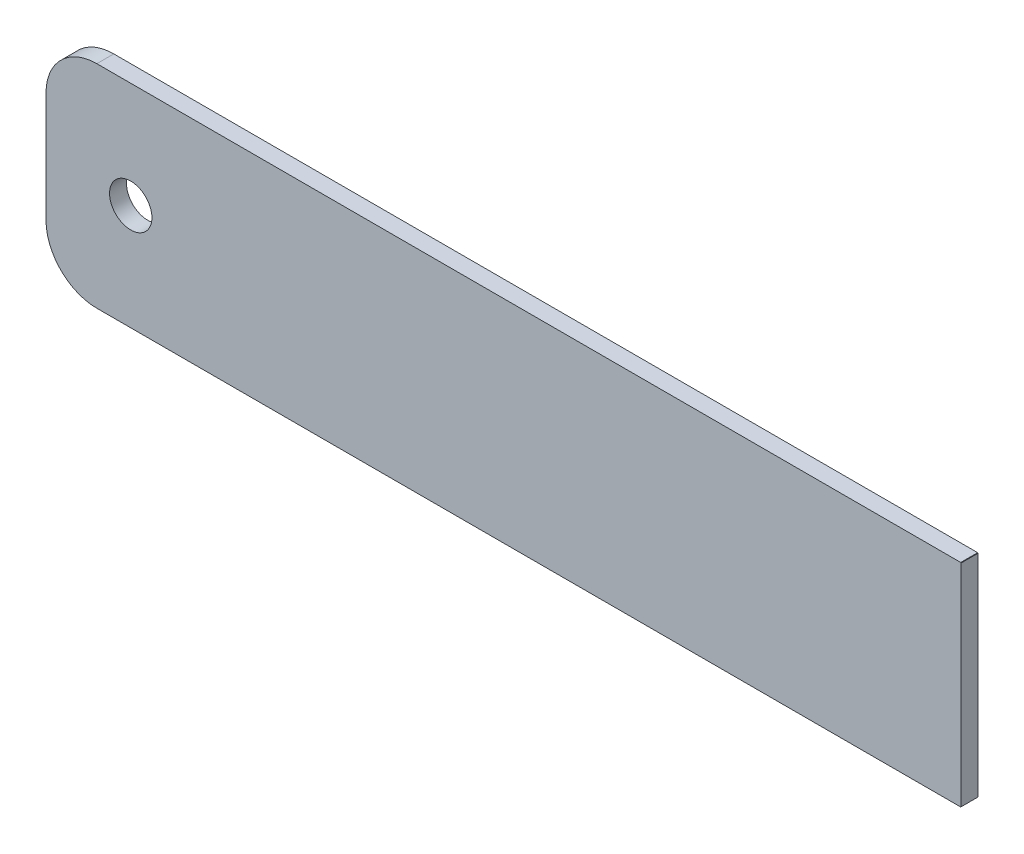
SolidWorks part; units mm, degrees
material "302 SSTL"
ref_plane "Front" through (0, 0, 0) normal (0, 0, 1) x (1, 0, 0)
ref_plane "Top" through (0, 0, 0) normal (0, 1, 0) x (1, 0, 0)
ref_plane "Right" through (0, 0, 0) normal (1, 0, 0) x (0, 0, -1)
sketch "Sketch1" plane through (0, 0, 0) normal (0, 0, 1) x (1, 0, 0)
  line L0 (0, 15.8496) -> (-0.0254, 15.875)
  line L1 (-0.0254, 0) -> (-64.77, 0)
  line L2 (0, 0.0254) -> (0, 15.8496)
  line L3 (-0.0254, 15.875) -> (-64.77, 15.875)
  line L4 (-68.58, 3.81) -> (-68.58, 12.065)
  line L5 (-0.0254, 0) -> (0, 0.0254)
  line L6 (-62.23, 7.9375) -> (0, 7.9375) construction
  circle A0 centre (-62.23, 7.9375) radius 1.5875
  arc A1 (-64.77, 15.875) -> (-68.58, 12.065) centre (-64.77, 12.065) ccw
  arc A2 (-64.77, 0) -> (-68.58, 3.81) centre (-64.77, 3.81) cw
  point P9 (-68.58, 15.875)
  point P12 (-68.58, 0)
  point P15 (0, 15.875)
  point P18 (0, 0)
  point P21 (0, 15.875)
  point P24 (0, 0)
  dimension "D3" = 6.35
  dimension "D4" = 3.175
  dimension "D5" = 3.81
  dimension "D1" = 15.875
  dimension "D2" = 68.58
  dimension "D9" = 0.0254
  dimension "D10" = 0.0254
extrude "Extrude1" add sketch "Sketch1" along normal blind 1.27
